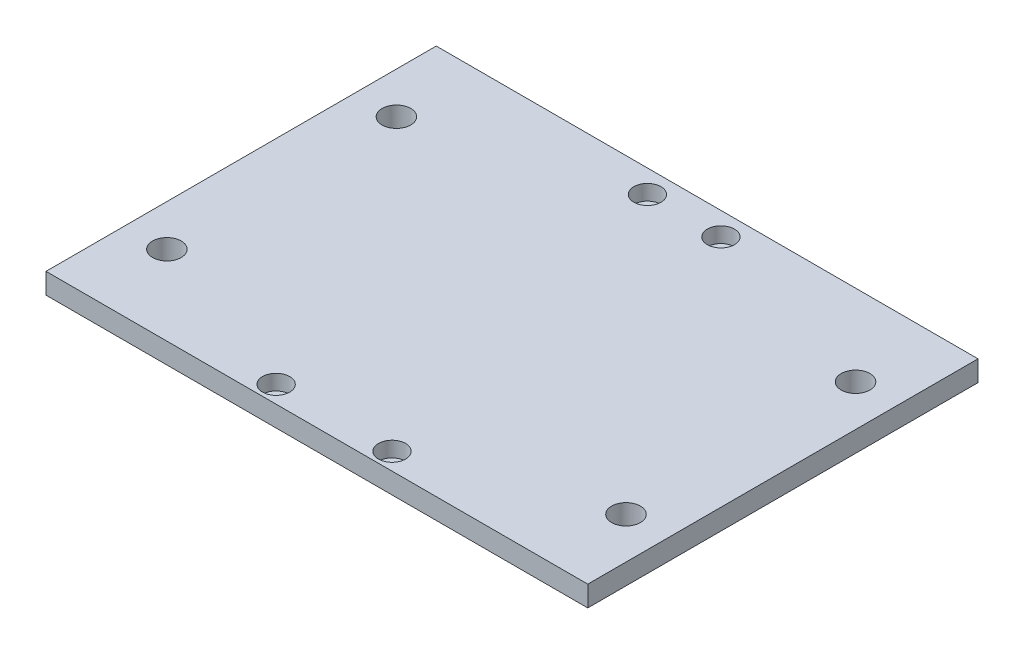
SolidWorks part; units mm, degrees
ref_plane "Front Plane" through (0, 0, 0) normal (0, 0, 1) x (1, 0, 0)
ref_plane "Top Plane" through (0, 0, 0) normal (0, 1, 0) x (1, 0, 0)
ref_plane "Right Plane" through (0, 0, 0) normal (1, 0, 0) x (0, 0, -1)
sketch "Sketch1" plane through (0, 0, 0) normal (0, 1, 0) x (1, 0, 0)
  line L1 (59.944, 43.18) -> (-59.944, 43.18)
  line L2 (59.944, 43.18) -> (59.944, -43.18)
  line L3 (59.944, -43.18) -> (-59.944, -43.18)
  line L4 (-59.944, 43.18) -> (-59.944, -43.18)
  line L5 (59.944, 43.18) -> (-59.944, -43.18) construction
  line L6 (59.944, -43.18) -> (-59.944, 43.18) construction
  point P0 (0, 0)
  dimension "D1" = 119.888
  dimension "D2" = 86.36
extrude "Boss-Extrude1" add sketch "Sketch1" along normal blind 4.572
hole_wizard "CBORE for M3 Hexagon socket head cap screws1" positions "Sketch2" profile "Sketch3" counterbore size "M3" standard "GB" end condition through all
sketch "Sketch2" plane through (0, 4.572, 0) normal (0, 1, 0) x (1, 0, 0)
  line L0 (-8.128, 38.1) -> (8.128, 38.1) construction
  line L2 (-12.827, -39.37) -> (12.827, -39.37) construction
  line L4 (0, 38.1) -> (0, -39.37) construction
  line L6 (59.944, 43.18) -> (-59.944, 43.18) construction
  point P0 (8.128, 38.1)
  point P2 (12.827, -39.37)
  point P4 (-12.827, -39.37)
  point P6 (-8.128, 38.1)
  dimension "D1" = 25.654
  dimension "D2" = 16.256
  dimension "3.05" = 77.47
  dimension "D4" = 5.08
sketch "Sketch3" plane through (8.128, 4.572, -38.1) normal (1, 0, 0) x (0, 0, 1)
  line L0 (0, 0) -> (0, 4.572)
  line L1 (0, 4.572) -> (1.7, 4.572)
  line L3 (1.7, 4.572) -> (1.7, 3.4)
  line L4 (1.7, 3.4) -> (3, 3.4)
  line L5 (3, 3.4) -> (3, 0)
  line L7 (3, 0) -> (0, 0)
  line L11 (0, -6.35) -> (0, 107.95) construction
  dimension "Thru Hole Dia." = 3.4
  dimension "Thru Hole Depth" = 4.572
  dimension "C'Bore Dia." = 6
  dimension "C'Bore Depth" = 3.4
sketch "Sketch5" plane through (0, 4.572, 0) normal (0, 1, 0) x (1, 0, 0)
  circle A0 centre (50.8, 25.2257) radius 3.175
  circle A1 centre (50.8, -25.5743) radius 3.175
  circle A2 centre (-50.8, 25.2257) radius 3.175
  circle A3 centre (-50.8, -25.5743) radius 3.175
  dimension "D1" = 6.35
  dimension "D2" = 6.35
  dimension "D3" = 6.35
  dimension "D4" = 6.35
  dimension "D5" = 50.8
  dimension "D6" = 50.8
  dimension "D7" = 50.8
extrude "Cut-Extrude1" cut sketch "Sketch5" against normal through all
